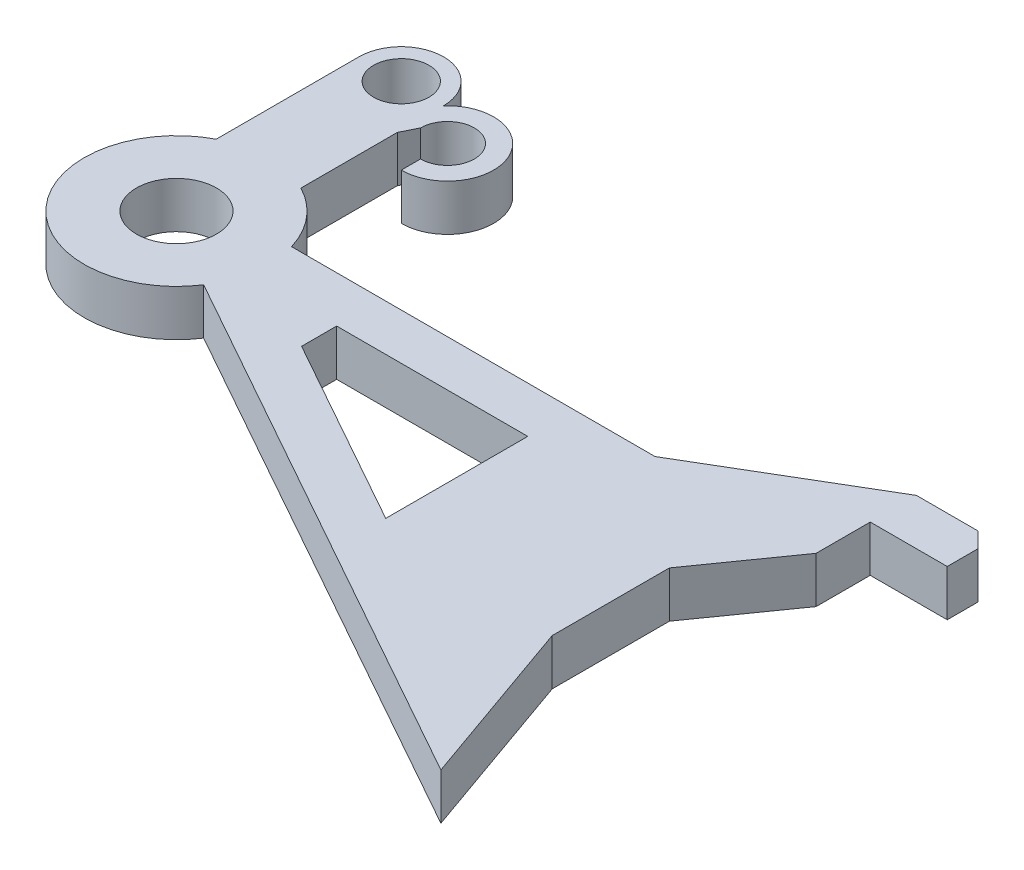
SolidWorks part; units mm, degrees
ref_plane "前视基准面" through (0, 0, 0) normal (0, 0, 1) x (1, 0, 0)
ref_plane "上视基准面" through (0, 0, 0) normal (0, 1, 0) x (1, 0, 0)
ref_plane "右视基准面" through (0, 0, 0) normal (1, 0, 0) x (0, 0, -1)
other "Configuration Table"
sketch "草图2" plane through (0, 0, 0) normal (0, 1, 0) x (1, 0, 0)
  circle A0 centre (0, 0) radius 2.6
  circle A1 centre (0, 0) radius 6
  dimension "D1" = 5.2
  dimension "D2" = 12
extrude "凸台-拉伸1" add sketch "草图2" along normal blind 3
sketch "草图3" plane through (0, 3, 0) normal (0, 1, 0) x (1, 0, 0)
  line L2 (-2.75, 14.6034) -> (-2.75, 5.3327)
  line L3 (-2.75, 5.3327) -> (2.75, 5.3327)
  line L4 (2.75, 14.6034) -> (2.75, 5.3327)
  circle A0 centre (0, 0) radius 6 construction
  circle A1 centre (0, 14.6034) radius 1.8
  arc A2 (2.75, 14.6034) -> (-2.75, 14.6034) centre (0, 14.6034) ccw
  dimension "D3" = 3.6
  dimension "D2" = 5.5
extrude "凸台-拉伸2" add sketch "草图3" against normal blind 3
sketch "草图5" plane through (0, 3, 0) normal (0, 1, 0) x (1, 0, 0)
  line L0 (3.25, 12.6034) -> (2.459, 11.0086)
  line L1 (5, 10.8534) -> (5, 9.6034)
  arc A0 (5, 10.8534) -> (3.25, 12.6034) centre (5, 12.6034) ccw
  arc A1 (5, 9.6034) -> (2.459, 11.0086) centre (5, 12.6034) ccw
  circle A2 centre (0, 14.6034) radius 1.8 construction
  dimension "D1" = 3.5
  dimension "D2" = 6
  dimension "D3" = 5
  dimension "D4" = 2
extrude "凸台-拉伸3" add sketch "草图5" against normal blind 3
sketch "草图6" plane through (0, 3, 0) normal (0, 1, 0) x (1, 0, 0)
  line L0 (5.0328, -3.2666) -> (40.0313, -22.8542)
  line L3 (29.3571, 1.7334) -> (5.0328, 1.7334)
  line L4 (5.0328, -3.2666) -> (5.0328, 1.7334)
  line L5 (36.7711, -3.0967) -> (5.0328, 1.7334) construction
  line L6 (40.0313, 1.5213) -> (5.0328, -3.2666) construction
  line L8 (29.3571, 1.7334) -> (40.0313, 8.0379)
  line L9 (40.0313, 5.0379) -> (40.0313, 1.5213)
  line L10 (40.0313, 1.5213) -> (36.0878, -4.0646)
  line L11 (40.0313, 8.0379) -> (45.0313, 8.0379)
  line L13 (40.0313, 5.0379) -> (45.0313, 5.0379)
  line L14 (45.0313, 8.0379) -> (45.0313, 5.0379)
  line L15 (36.0878, -4.0646) -> (36.0878, -11.6784)
  line L16 (36.0878, -11.6784) -> (40.0313, -22.8542)
  arc A0 (-2.75, 5.3327) -> (2.75, 5.3327) centre (0, 0) ccw construction
  point P0 (22.3345, -0.8997)
  dimension "D2" = 5
  dimension "D3" = 3
  dimension "D4" = 5
extrude "凸台-拉伸4" add sketch "草图6" against normal blind 3
chamfer "倒角2" distance 1 angle 45 1 edges at (45.0313, 1.5, -8.0379)
sketch "草图7" plane through (0, 3, 0) normal (0, 1, 0) x (1, 0, 0)
  line L0 (11.6738, -3.5455) -> (24.0878, -10.4932)
  line L1 (24.0878, -10.4932) -> (24.0878, -1.2666)
  line L2 (24.0878, -1.2666) -> (11.6738, -1.2666)
  line L3 (11.6738, -1.2666) -> (11.6738, -3.5455)
  line L4 (29.3571, 1.7334) -> (5.7442, 1.7334) construction
  line L5 (5.0328, -3.2666) -> (40.0313, -22.8542) construction
  line L6 (36.0878, -11.6784) -> (36.0878, -4.0646) construction
  arc A0 (5.7442, 1.7334) -> (2.75, 5.3327) centre (0, 0) ccw construction
  dimension "D1" = 3
  dimension "D2" = 3
  dimension "D3" = 12
  dimension "D4" = 11.6738
extrude "切除-拉伸1" cut sketch "草图7" against normal mid plane 10
